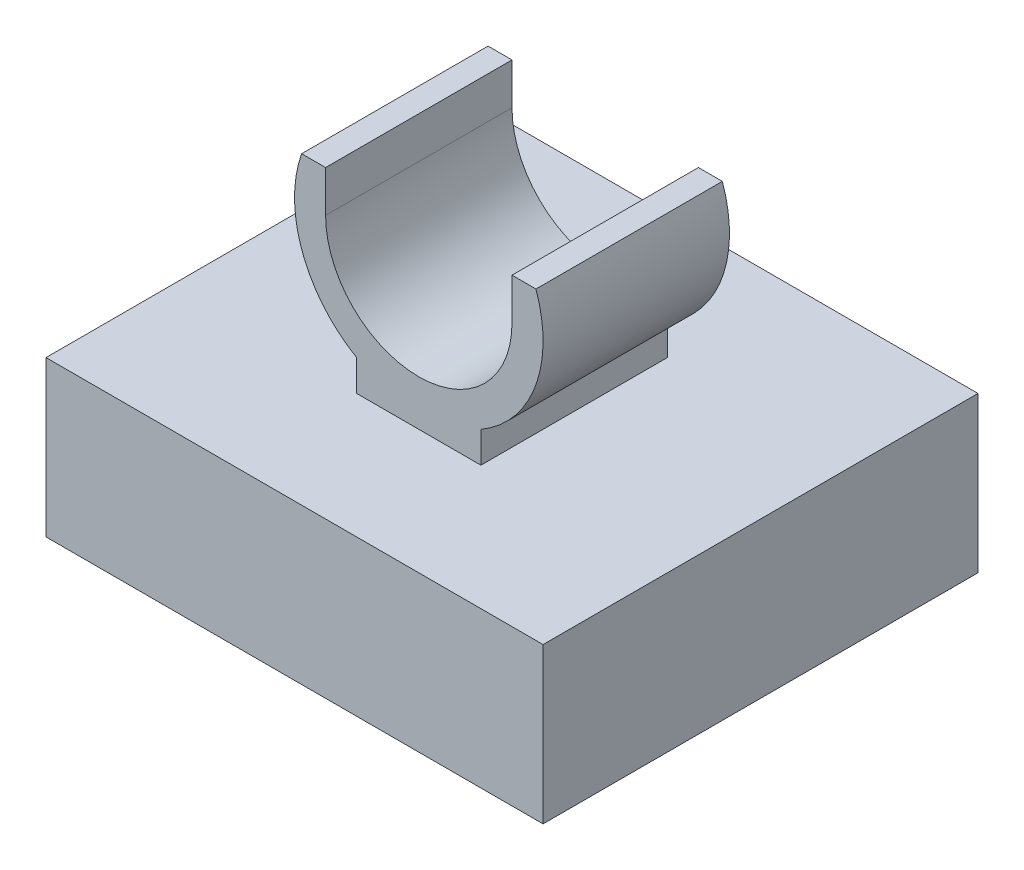
SolidWorks part; units mm, degrees
material "ABS"
ref_plane "Front Plane" through (0, 0, 0) normal (0, 0, 1) x (1, 0, 0)
ref_plane "Top Plane" through (0, 0, 0) normal (0, 1, 0) x (1, 0, 0)
ref_plane "Right Plane" through (0, 0, 0) normal (1, 0, 0) x (0, 0, -1)
sketch "Sketch1" plane through (0, 0, 0) normal (0, 0, 1) x (1, 0, 0)
  line L0 (-5.08, 0) -> (5.08, 0)
  line L1 (5.08, 0) -> (5.08, -3.175)
  line L2 (5.08, -3.175) -> (-5.08, -3.175)
  line L3 (-5.08, -3.175) -> (-5.08, 0)
  point P3 (0, -3.175)
  dimension "D1" = 10.16
  dimension "D2" = 3.175
extrude "Boss-Extrude1" add sketch "Sketch1" along normal mid plane 8.89
sketch "Sketch2" plane through (0, 0, 0) normal (0, 0, 1) x (1, 0, 0)
  line L0 (-1.905, 2.8347) -> (-1.905, 3.6814)
  line L1 (1.905, 2.8347) -> (1.905, 3.6814)
  line L2 (-2.3947, 3.6814) -> (-1.905, 3.6814)
  line L3 (1.905, 3.6814) -> (2.3947, 3.6814)
  line L4 (-1.27, 0.635) -> (-1.27, 0)
  line L5 (5.08, 0) -> (-5.08, 0) construction
  line L6 (1.27, 0.635) -> (1.27, 0)
  line L7 (-1.27, 0) -> (1.27, 0)
  arc A0 (-2.3947, 3.6814) -> (-1.27, 0.635) centre (0, 2.8347) ccw
  arc A1 (-1.905, 2.8347) -> (1.905, 2.8347) centre (0, 2.8347) ccw
  arc A2 (1.27, 0.635) -> (2.3947, 3.6814) centre (0, 2.8347) ccw
  dimension "D1" = 5.08
  dimension "D2" = 3.81
  dimension "D3" = 0.635
extrude "Boss-Extrude2" add sketch "Sketch2" along normal mid plane 3.81
sketch "Sketch3" plane through (0, -3.175, 0) normal (0, -1, 0) x (1, 0, 0)
  line L0 (-2.54, 2.54) -> (-2.54, -2.54)
  line L1 (-2.54, -2.54) -> (2.54, -2.54)
  line L2 (2.54, -2.54) -> (2.54, 2.54)
  line L3 (2.54, 2.54) -> (-2.54, 2.54)
  line L4 (-5.08, -4.445) -> (5.08, -4.445)
  line L5 (5.08, -4.445) -> (5.08, 4.445)
  line L6 (5.08, 4.445) -> (-5.08, 4.445)
  line L7 (-5.08, 4.445) -> (-5.08, -4.445)
  line L8 (-5.08, -4.445) -> (5.08, -4.445)
  line L9 (5.08, -4.445) -> (5.08, 4.445)
  line L10 (5.08, 4.445) -> (-5.08, 4.445)
  line L11 (-5.08, 4.445) -> (-5.08, -4.445)
  dimension "D1" = 0
extrude "Cut-Extrude1" cut sketch "Sketch3" against normal blind 1.905 flip side to cut
